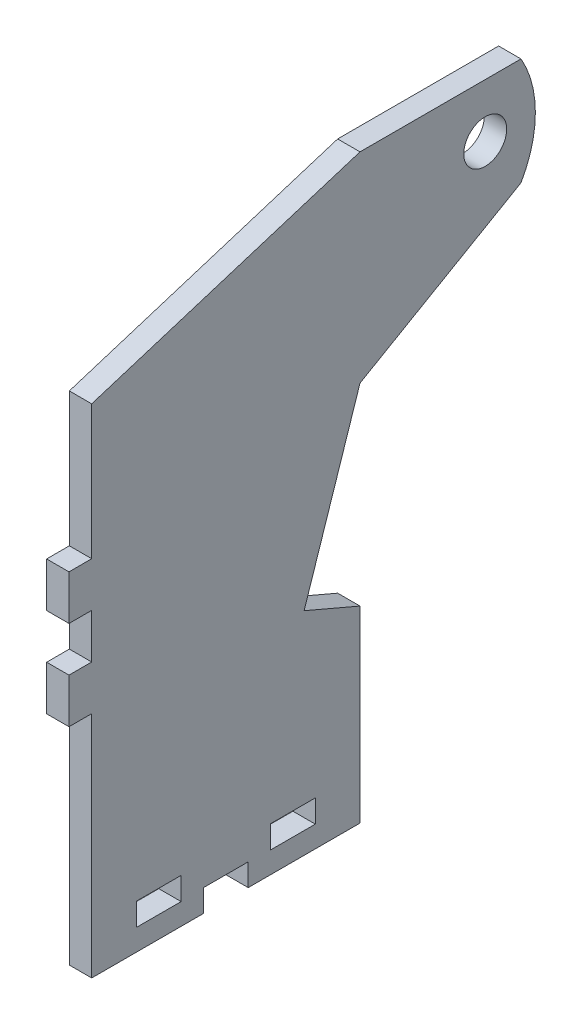
SolidWorks part; units mm, degrees
ref_plane "Front Plane" through (0, 0, 0) normal (0, 0, 1) x (1, 0, 0)
ref_plane "Top Plane" through (0, 0, 0) normal (0, 1, 0) x (1, 0, 0)
ref_plane "Right Plane" through (0, 0, 0) normal (1, 0, 0) x (0, 0, -1)
sketch "Sketch1" plane through (0, 0, 0) normal (1, 0, 0) x (0, 0, -1)
  line L0 (-8.9013, 27.9173) -> (29.1987, 27.9173)
  line L1 (-8.9013, -54.6327) -> (29.1987, -54.6327)
  line L2 (-8.9013, -54.6327) -> (-8.9013, 27.9173)
  line L3 (29.1987, 27.9173) -> (52.0587, 27.9173)
  line L4 (29.1987, -54.6327) -> (29.1987, -0.5209)
  line L7 (52.0587, 27.9173) -> (52.0587, 12.6773) construction
  line L8 (52.0587, 12.6773) -> (29.1987, -0.5209)
  arc A0 (52.0587, 27.9173) -> (52.0587, 12.6773) centre (38.8604, 20.2973) cw
  point P0 (0, 0)
  dimension "D4" = 15.24
  dimension "D5" = 120
  dimension "D3" = 38.1
  dimension "D6" = 15.24
  dimension "D1" = 38.1
  dimension "D2" = 82.55
  dimension "D7" = 22.86
extrude "Boss-Extrude1" add sketch "Sketch1" along normal blind 3.175
sketch "Sketch3" plane through (3.175, 0, 0) normal (1, 0, 0) x (0, 0, -1)
  line L2 (-8.9013, 27.9173) -> (-8.9013, -54.6327) construction
  line L3 (52.0587, 27.9173) -> (-8.9013, 27.9173) construction
  circle A0 centre (46.9787, 20.2973) radius 3.048
  dimension "D1" = 7.62
  dimension "D3" = 6.096
  dimension "D2" = 55.88
extrude "cut for axle" cut sketch "Sketch3" against normal through all
sketch "Sketch4" plane through (3.175, 0, 0) normal (1, 0, 0) x (0, 0, -1)
  line L0 (10.1487, -54.6327) -> (10.1487, -49.9718) construction
  line L1 (-2.5513, -51.5847) -> (3.7987, -51.5847)
  line L2 (-2.5513, -51.5847) -> (-2.5513, -48.3589)
  line L3 (-2.5513, -48.3589) -> (3.7987, -48.3589)
  line L4 (3.7987, -51.5847) -> (3.7987, -48.3589)
  line L5 (-2.5513, -51.5847) -> (3.7987, -48.3589) construction
  line L6 (-2.5513, -48.3589) -> (3.7987, -51.5847) construction
  line L7 (16.4987, -51.5847) -> (22.8487, -51.5847)
  line L8 (16.4987, -51.5847) -> (16.4987, -48.3589)
  line L9 (16.4987, -48.3589) -> (22.8487, -48.3589)
  line L10 (22.8487, -51.5847) -> (22.8487, -48.3589)
  line L11 (16.4987, -51.5847) -> (22.8487, -48.3589) construction
  line L12 (16.4987, -48.3589) -> (22.8487, -51.5847) construction
  line L13 (-8.9013, -54.6327) -> (29.1987, -54.6327) construction
  line L14 (10.1487, -49.9718) -> (3.7987, -49.9718) construction
  line L15 (10.1487, -49.9718) -> (16.4987, -49.9718) construction
  line L16 (-8.9013, -54.6327) -> (29.1987, -54.6327) construction
  line L17 (10.1487, -54.6327) -> (6.9737, -54.6327)
  line L18 (6.9737, -54.6327) -> (6.9737, -51.4577)
  line L19 (6.9737, -51.4577) -> (13.3237, -51.4577)
  line L20 (13.3237, -51.4577) -> (13.3237, -54.6327)
  line L21 (13.3237, -54.6327) -> (10.1487, -54.6327)
  point P0 (0.6237, -49.9718)
  point P5 (19.6737, -49.9718)
  dimension "D1" = 6.35
  dimension "D2" = 3.048
  dimension "D3" = 6.35
  dimension "D4" = 6.35
  dimension "D5" = 3.2258
  dimension "D6" = 3.2258
  dimension "D7" = 6.35
  dimension "D8" = 3.175
extrude "cut for tabs" cut sketch "Sketch4" against normal through all
sketch "Sketch6" plane through (3.175, 0, 0) normal (1, 0, 0) x (0, 0, -1)
  line L0 (29.1987, -0.5209) -> (21.257, -24.5435)
  line L2 (21.257, -24.5435) -> (29.1987, -27.9395)
  line L5 (29.1987, -54.6327) -> (29.1987, -0.5209) construction
  line L6 (29.1987, -27.9395) -> (29.1987, -0.5209)
extrude "cut for clearance" cut sketch "Sketch6" against normal through all
sketch "Sketch9" plane through (0, 0, 0) normal (-1, 0, 0) x (0, 0, 1)
  line L0 (8.9013, 27.9173) -> (-29.1987, 27.9173)
  line L1 (-52.0587, 27.9173) -> (8.9013, 27.9173) construction
  line L2 (8.9013, 27.9173) -> (8.9013, 15.9793)
  line L3 (8.9013, 27.9173) -> (8.9013, -54.6327) construction
  line L4 (-29.1987, 27.9173) -> (8.9013, 15.9793)
  dimension "D1" = 11.938
  dimension "D2" = 38.1
extrude "Cut-Extrude1" cut sketch "Sketch9" against normal through all
sketch "Sketch10" plane through (0, 0, 0) normal (-1, 0, 0) x (0, 0, 1)
  line L0 (8.9013, -3.0707) -> (12.1271, -3.0707)
  line L1 (8.9013, 15.9793) -> (8.9013, -54.6327) construction
  line L2 (12.1271, -3.0707) -> (12.1271, -9.4207)
  line L3 (12.1271, -9.4207) -> (8.9013, -9.4207)
  line L4 (8.9013, -9.4207) -> (8.9013, -3.0707)
  line L5 (8.9013, -15.7707) -> (12.1271, -15.7707)
  line L6 (12.1271, -15.7707) -> (12.1271, -22.1207)
  line L7 (12.1271, -22.1207) -> (8.9013, -22.1207)
  line L8 (8.9013, -22.1207) -> (8.9013, -15.7707)
  dimension "D1" = 3.2258
  dimension "D2" = 3.2258
  dimension "D3" = 6.35
  dimension "D4" = 6.35
  dimension "D5" = 6.35
  dimension "D6" = 19.05
extrude "tabs for back plate" add sketch "Sketch10" against normal blind 3.175
